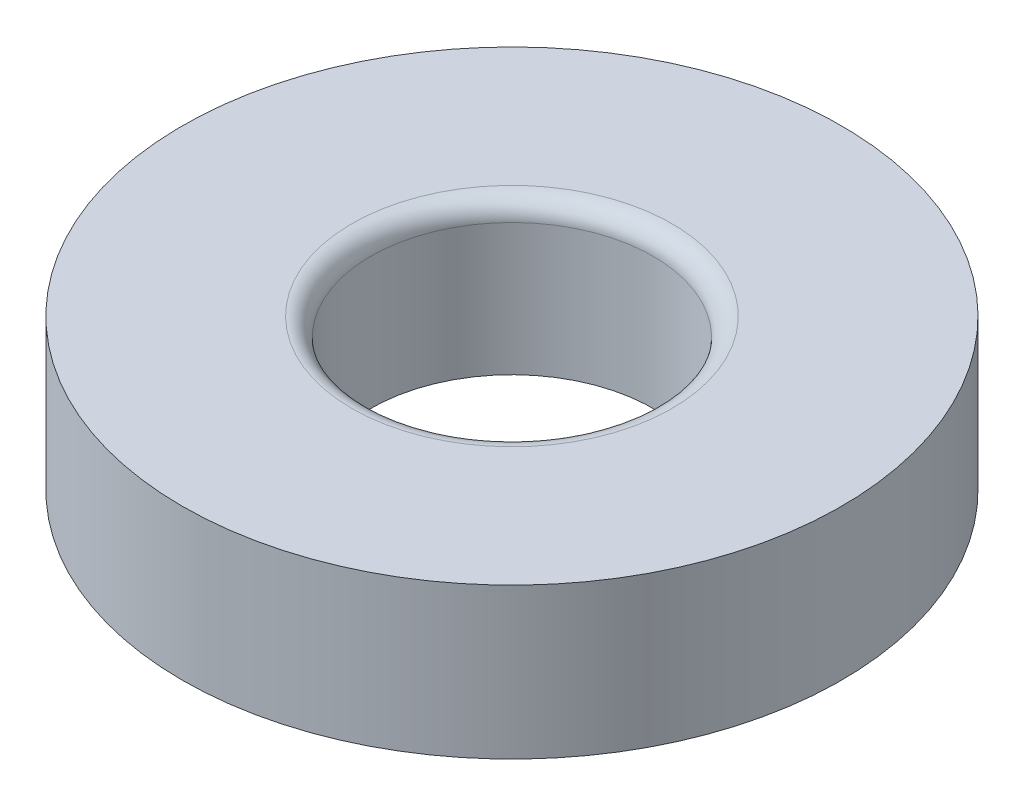
SolidWorks part; units mm, degrees
ref_plane "Front Plane" through (0, 0, 0) normal (0, 0, 1) x (1, 0, 0)
ref_plane "Top Plane" through (0, 0, 0) normal (0, 1, 0) x (1, 0, 0)
ref_plane "Right Plane" through (0, 0, 0) normal (1, 0, 0) x (0, 0, -1)
sketch "Sketch1" plane through (0, 0, 0) normal (0, 1, 0) x (1, 0, 0)
  circle A0 centre (0, 0) radius 17.5
extrude "Boss-Extrude1" add sketch "Sketch1" along normal blind 8 separate body
sketch "Sketch2" plane through (0, 8, 0) normal (0, 1, 0) x (1, 0, 0)
  circle A0 centre (0, 0) radius 7.5
extrude "Cut-Extrude1" cut sketch "Sketch2" against normal through all
fillet "Fillet1" radius 1 1 edges at (0, 8, 7.5)
